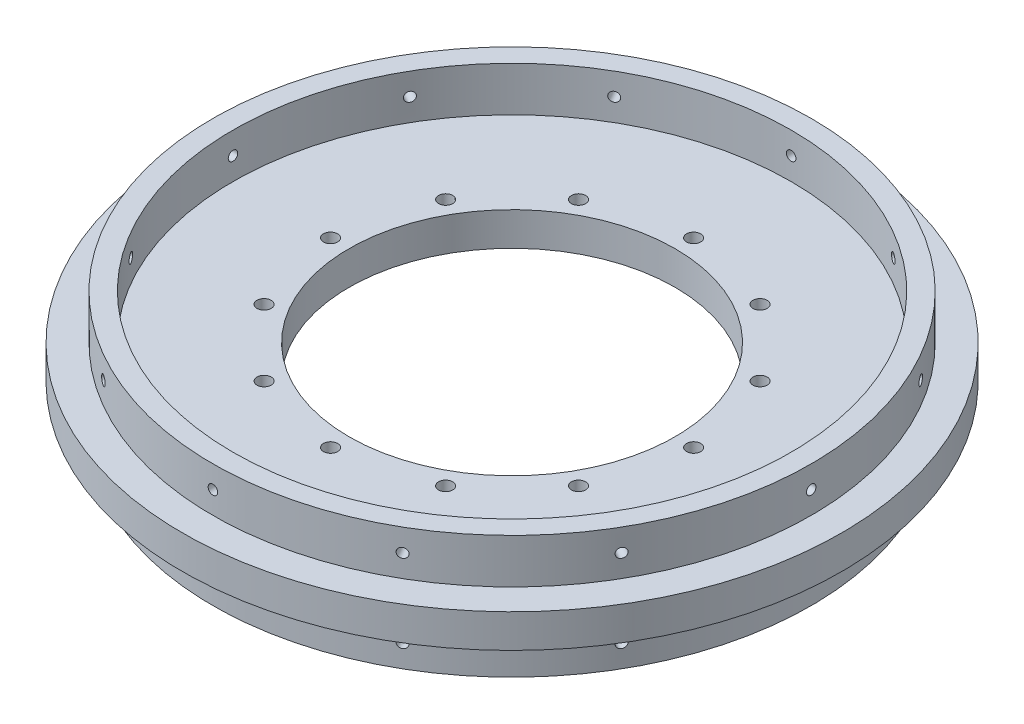
SolidWorks part; units mm, degrees
material "6061-T6 (SS)"
ref_plane "Front Plane" through (0, 0, 0) normal (0, 0, 1) x (1, 0, 0)
ref_plane "Top Plane" through (0, 0, 0) normal (0, 1, 0) x (1, 0, 0)
ref_plane "Right Plane" through (0, 0, 0) normal (1, 0, 0) x (0, 0, -1)
sketch "Sketch1" plane through (0, 0, 0) normal (0, 1, 0) x (1, 0, 0)
  line L5 (0, 0) -> (127.635, 0)
  line L6 (0, 0) -> (0, 127.635)
  line L7 (0, 127.635) -> (127.635, 127.635)
  line L8 (127.635, 0) -> (127.635, 127.635)
  dimension "D1" = 127.635
  dimension "D2" = 127.635
extrude "Boss-Extrude1" add sketch "Sketch1" along normal blind 9.525 contours L5 L8 L7 L6
sketch "Sketch12" plane through (0, 0, 0) normal (0, -1, 0) x (1, 0, 0)
  line L0 (63.8175, 0) -> (63.8175, -127.635) construction
  line L1 (0, 0) -> (127.635, 0) construction
  line L2 (0, -127.635) -> (127.635, -127.635) construction
  line L3 (0, -63.8175) -> (127.635, -63.8175) construction
  line L4 (0, 0) -> (0, -127.635) construction
  line L5 (127.635, 0) -> (127.635, -127.635) construction
  circle A0 centre (63.8175, -63.8175) radius 93.726
  dimension "D1" = 187.452
extrude "Boss-Extrude2" add sketch "Sketch12" against normal up to surface (9.525 mm away) contours A0 up to face at (63.8175, 9.525, -63.8175)
sketch "Sketch5" plane through (0, 9.525, 0) normal (0, 1, 0) x (1, 0, 0)
  circle A0 centre (63.8175, 63.8175) radius 46.355
  circle A3 centre (63.8175, 63.8175) radius 93.726 construction
  dimension "D1" = 92.71
extrude "Cut-Extrude1" cut sketch "Sketch5" against normal blind 9.525
sketch "Sketch11" plane through (0, 9.525, 0) normal (0, 1, 0) x (1, 0, 0)
  line L0 (63.8175, 63.8175) -> (63.8175, 115.443) construction
  circle A0 centre (63.8175, 115.443) radius 2.0193
  dimension "D2" = 4.0386
  dimension "D1" = 51.6255
extrude "Cut-Extrude3" cut sketch "Sketch11" against normal through all contours A0
pattern_circular "CirPattern1" count 12 over 360 about axis through (63.8175, 0, -63.8175) along (0, 1, 0) of "Cut-Extrude3"
sketch "Sketch14" plane through (0, 9.525, 0) normal (0, -1, 0) x (1, 0, 0)
  line L0 (63.8175, -63.8175) -> (147.6375, -63.8175) construction
  line L1 (0, -5.2388) -> (0, 5.2388) construction
  line L2 (147.6375, -63.8175) -> (152.7175, -63.8175)
  line L3 (136.3808, -105.7742) -> (140.8401, -108.2104)
  circle A0 centre (63.8175, -63.8175) radius 46.355 construction
  arc A2 (147.6375, -63.8175) -> (136.3808, -105.7742) centre (63.8175, -63.8175) cw
  arc A3 (152.7175, -63.8175) -> (140.8401, -108.2104) centre (63.8175, -63.8175) cw
  point P0 (63.8175, -63.8175)
  dimension "D1" = 83.82
  dimension "D2" = 88.9
  dimension "D3" = 46.482
  dimension "D4" = 43.942
ref_plane "Support mirror reference plane" through (0, 4.7625, 0) normal (0, 1, 0) x (1, 0, 0)
sketch "Sketch25" plane through (0, 9.525, 0) normal (0, -1, 0) x (1, 0, 0)
  line L0 (63.8175, -63.8175) -> (123.0872, -4.5478) construction
  line L2 (123.0872, -4.5478) -> (126.6793, -0.9557)
  line L3 (144.7953, -42.1754) -> (149.6712, -40.7448)
  line L5 (63.8175, -63.8175) -> (147.6375, -63.8175) construction
  arc A2 (123.0872, -4.5478) -> (144.7953, -42.1754) centre (63.8175, -63.8175) cw
  arc A3 (126.6793, -0.9557) -> (149.6712, -40.7448) centre (63.8175, -63.8175) cw
  point P0 (63.8175, -63.8175)
  dimension "D1" = 83.82
  dimension "D2" = 88.9
  dimension "D3" = 46.482
  dimension "D4" = 43.942
  dimension "D5" = 45
sketch "Sketch30" plane through (0, 0, 0) normal (0, -1, 0) x (1, 0, 0)
  circle A0 centre (63.8175, -63.8175) radius 85.09
  circle A1 centre (63.8175, -63.8175) radius 79.375
  dimension "D1" = 170.18
  dimension "D2" = 158.75
extrude "Boss-Extrude3" add sketch "Sketch30" along normal blind 12.7
mirror "Mirror1" about plane through (0, 4.7625, 0) normal (0, 1, 0) of "Boss-Extrude3"
sketch "Sketch31" plane through (0, 0, 0) normal (0, -1, 0) x (-1, 0, 0)
  line L0 (-63.8175, -52.481) -> (-63.8175, 177.7216) construction
ref_plane "Plane1" through (0, 0, -148.9075) normal (0, 0, -1) x (-1, 0, 0)
ref_plane "Plane2" through (63.8175, 0, 0) normal (-1, 0, 0) x (0, 0, -1)
sketch "Sketch32" plane through (0, 0, -148.9075) normal (0, 0, -1) x (-1, 0, 0)
  line L4 (-63.8175, -87.3125) -> (-63.8175, 87.3125) construction
  line L5 (-148.9075, 0) -> (21.2725, 0) construction
  line L6 (21.2725, 9.525) -> (-148.9075, 9.525) construction
  circle A0 centre (-63.8175, -6.35) radius 1.3526
  circle A1 centre (-63.8175, 15.875) radius 1.3525
  dimension "D1" = 2.7051
  dimension "D2" = 2.7051
  dimension "D3" = 6.35
  dimension "D4" = 6.35
extrude "Cut-Extrude4" cut sketch "Sketch32" against normal blind 15.24
pattern_circular "CirPattern2" count 12 over 360 about axis through (63.8175, -12.7, -63.8175) along (0, 1, 0) of "Cut-Extrude4"
